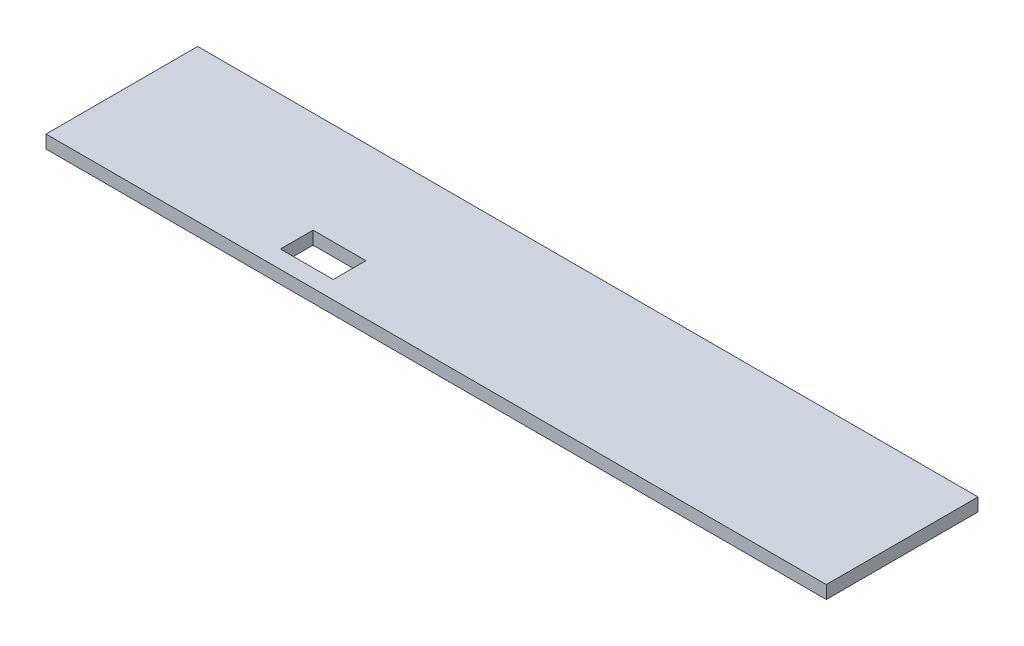
SolidWorks part; units mm, degrees
ref_plane "Front Plane" through (0, 0, 0) normal (0, 0, 1) x (1, 0, 0)
ref_plane "Top Plane" through (0, 0, 0) normal (0, 1, 0) x (1, 0, 0)
ref_plane "Right Plane" through (0, 0, 0) normal (1, 0, 0) x (0, 0, -1)
sketch "Sketch1" plane through (0, 0, 0) normal (0, 1, 0) x (1, 0, 0)
  line L1 (-104.6869, 23.6057) -> (75.3131, 23.6057)
  line L2 (-104.6869, 23.6057) -> (-104.6869, 58.6057)
  line L3 (-104.6869, 58.6057) -> (75.3131, 58.6057)
  line L4 (75.3131, 23.6057) -> (75.3131, 58.6057)
  dimension "D1" = 180
  dimension "D2" = 35
extrude "Boss-Extrude1" add sketch "Sketch1" along normal blind 3
sketch "Sketch2" plane through (0, 3, 0) normal (0, 1, 0) x (1, 0, 0)
  line L0 (-104.6869, 58.6057) -> (-104.6869, 23.6057) construction
  line L1 (-54.6869, 35.2057) -> (-42.4869, 35.2057)
  line L2 (-54.6869, 35.2057) -> (-54.6869, 27.6757)
  line L3 (-54.6869, 27.6757) -> (-42.4869, 27.6757)
  line L4 (-42.4869, 35.2057) -> (-42.4869, 27.6757)
  line L5 (-104.6869, 23.6057) -> (75.3131, 23.6057) construction
  dimension "D1" = 50
  dimension "D2" = 12.2
  dimension "D3" = 4.07
  dimension "D4" = 7.53
extrude "Cut-Extrude1" cut sketch "Sketch2" against normal through all
